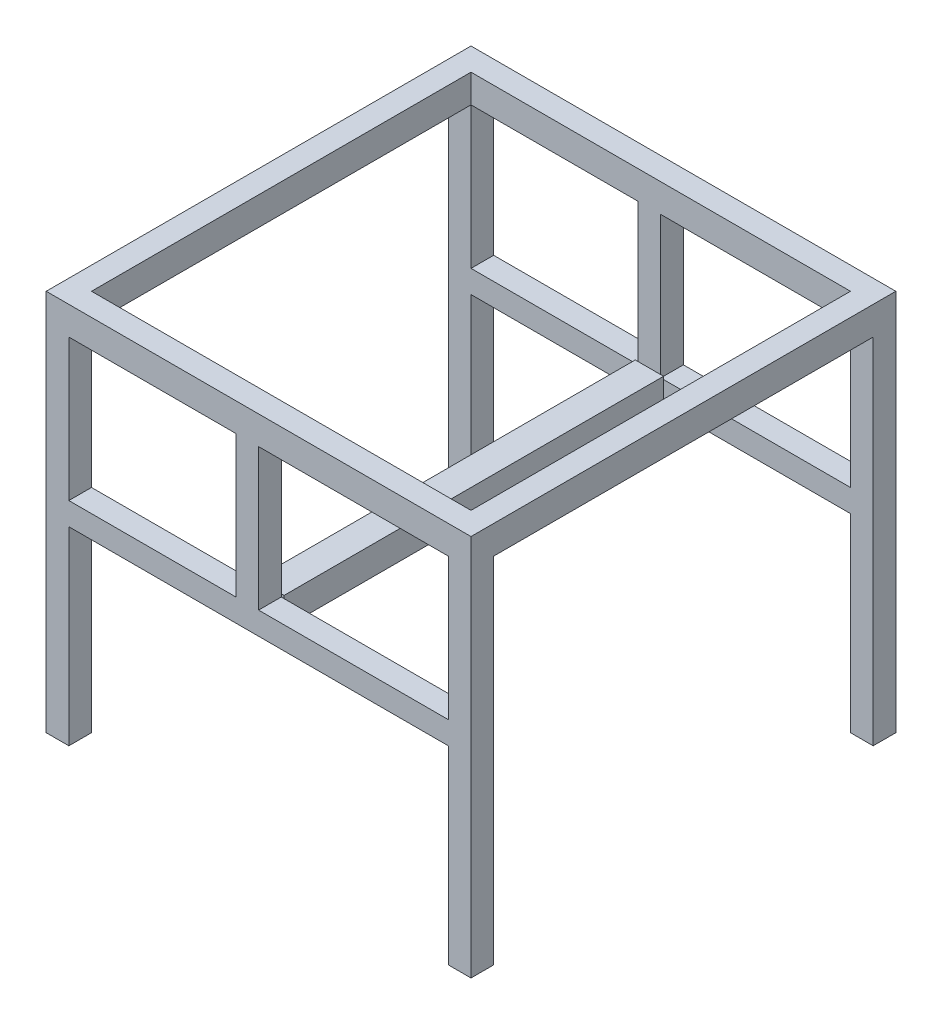
SolidWorks part; units mm, degrees
ref_plane "Front Plane" through (0, 0, 0) normal (0, 0, 1) x (1, 0, 0)
ref_plane "Top Plane" through (0, 0, 0) normal (0, 1, 0) x (1, 0, 0)
ref_plane "Right Plane" through (0, 0, 0) normal (1, 0, 0) x (0, 0, -1)
sketch "Sketch1" plane through (0, 0, 0) normal (0, 1, 0) x (1, 0, 0)
  line L1 (-150, 150) -> (150, 150)
  line L2 (-150, 150) -> (-150, -150)
  line L3 (-150, -150) -> (150, -150)
  line L4 (150, 150) -> (150, -150)
  line L5 (-134, -134) -> (134, -134)
  line L6 (-134, -134) -> (-134, 134)
  line L7 (-134, 134) -> (134, 134)
  line L8 (134, -134) -> (134, 134)
  point P8 (0, 150)
  point P10 (150, 0)
  dimension "D1" = 300
  dimension "D2" = 300
  dimension "D3" = 16
  dimension "D4" = 16
  dimension "D5" = 16
  dimension "D6" = 16
extrude "Boss-Extrude1" add sketch "Sketch1" along normal blind 20
sketch "Sketch3" plane through (0, 0, 150) normal (0, 0, 1) x (1, 0, 0)
  line L1 (0, 0) -> (-16, 0)
  line L2 (0, 0) -> (0, -100)
  line L3 (0, -100) -> (-16, -100)
  line L4 (-16, 0) -> (-16, -100)
  dimension "D1" = 16
  dimension "D2" = 100
extrude "Boss-Extrude2" add sketch "Sketch3" against normal up to surface (16 mm away) up to face at (0, 10, 134)
sketch "Sketch4" plane through (0, 0, 150) normal (0, 0, 1) x (1, 0, 0)
  line L1 (-150, 0) -> (-134, 0)
  line L2 (-150, 0) -> (-150, -250)
  line L3 (-150, -250) -> (-134, -250)
  line L4 (-134, 0) -> (-134, -250)
  line L5 (150, 0) -> (134, 0)
  line L6 (150, 0) -> (150, -250)
  line L7 (150, -250) -> (134, -250)
  line L8 (134, 0) -> (134, -250)
  dimension "D1" = 16
  dimension "D2" = 16
  dimension "D3" = 250
  dimension "D4" = 250
extrude "Boss-Extrude3" add sketch "Sketch4" against normal up to surface (16 mm away) up to face at (-4, -20, 134)
sketch "Sketch5" plane through (0, 0, 150) normal (0, 0, 1) x (1, 0, 0)
  line L0 (-134, -250) -> (-134, 0) construction
  line L1 (-134, -100) -> (134, -100)
  line L2 (-134, -100) -> (-134, -116)
  line L3 (-134, -116) -> (134, -116)
  line L4 (134, -100) -> (134, -116)
  line L5 (134, 0) -> (134, -250) construction
  line L6 (-16, -100) -> (0, -100) construction
  point P8 (0, -100)
  dimension "D1" = 16
extrude "Boss-Extrude4" add sketch "Sketch5" against normal up to surface (16 mm away) up to face at (142, -125, 134)
mirror "Mirror1" about plane through (0, 0, 0) normal (0, 0, 1) of "Boss-Extrude4", "Boss-Extrude3", "Boss-Extrude2"
sketch "Sketch6" plane through (0, 0, 134) normal (0, 0, -1) x (-1, 0, 0)
  line L1 (-2, -98) -> (18, -98)
  line L2 (-2, -98) -> (-2, -118)
  line L3 (-2, -118) -> (18, -118)
  line L4 (18, -98) -> (18, -118)
  line L5 (30, -100) -> (30, -116) construction
  line L6 (16, -100) -> (134, -100) construction
  line L7 (134, -116) -> (-134, -116) construction
  line L8 (16, -80) -> (0, -80) construction
  line L9 (16, 0) -> (16, -100) construction
  line L10 (0, -100) -> (0, 0) construction
  line L11 (134, 20) -> (-134, 20) construction
  line L12 (150, 0) -> (150, -250) construction
  point P20 (8, -80)
  point P21 (8, -98)
  point P22 (30, -108)
  point P23 (18, -108)
  dimension "D1" = 20
  dimension "D2" = 20
  dimension "D3" = 100
  dimension "D4" = 120
extrude "Boss-Extrude5" add sketch "Sketch6" along normal up to surface (268 mm away) up to face at (-1.6, -79.6, -134)
